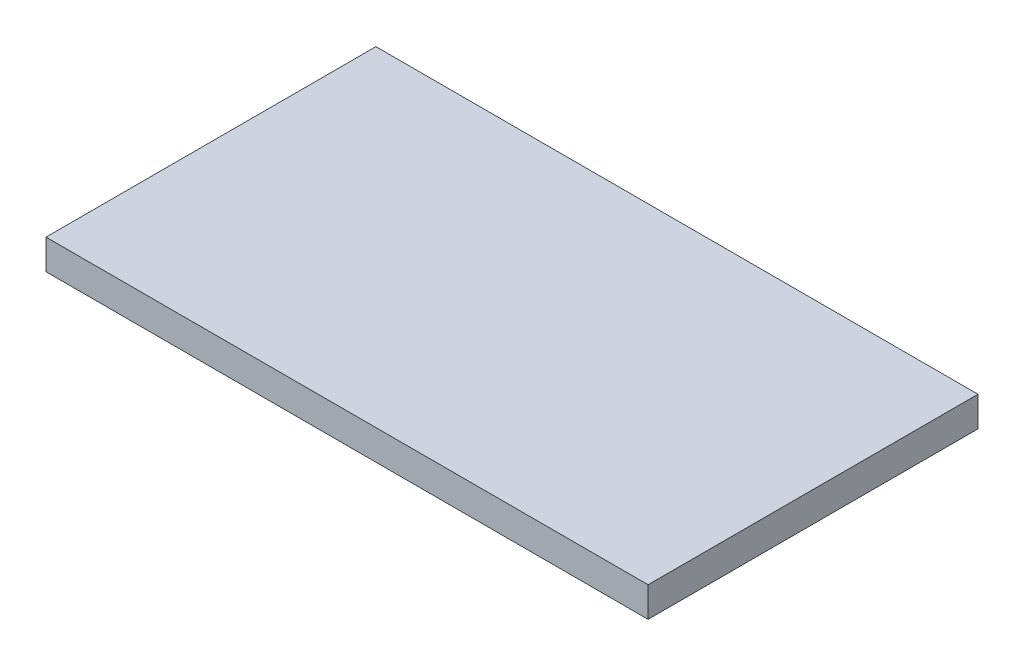
SolidWorks part; units mm, degrees
ref_plane "Front Plane" through (0, 0, 0) normal (0, 0, 1) x (1, 0, 0)
ref_plane "Top Plane" through (0, 0, 0) normal (0, 1, 0) x (1, 0, 0)
ref_plane "Right Plane" through (0, 0, 0) normal (1, 0, 0) x (0, 0, -1)
sketch "Sketch1" plane through (0, 0, 0) normal (0, 1, 0) x (1, 0, 0)
  line L1 (0, 0) -> (200.75, 0)
  line L2 (0, 0) -> (0, -110)
  line L3 (0, -110) -> (200.75, -110)
  line L4 (200.75, 0) -> (200.75, -110)
  dimension "D1" = 110
  dimension "D2" = 200.75
extrude "Boss-Extrude1" add sketch "Sketch1" along normal blind 10
